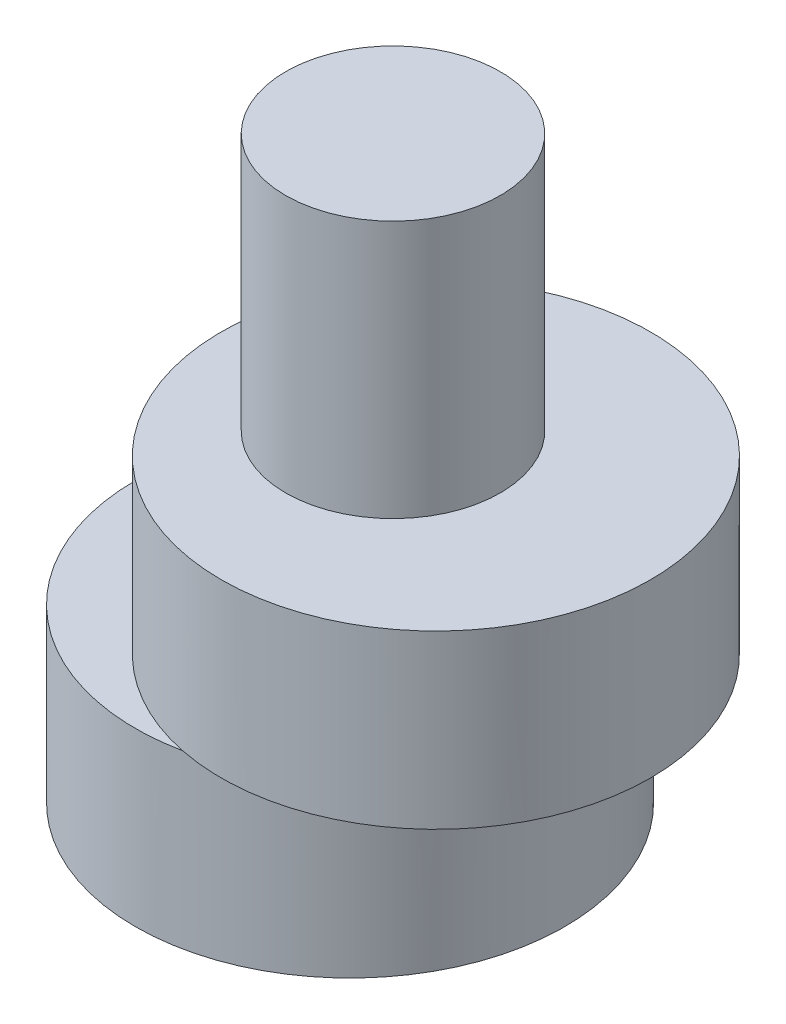
SolidWorks part; units mm, degrees
ref_plane "Front Plane" through (0, 0, 0) normal (0, 0, 1) x (1, 0, 0)
ref_plane "Top Plane" through (0, 0, 0) normal (0, 1, 0) x (1, 0, 0)
ref_plane "Right Plane" through (0, 0, 0) normal (1, 0, 0) x (0, 0, -1)
sketch "Sketch1" plane through (0, 0, 0) normal (0, 1, 0) x (1, 0, 0)
  line L0 (0, 0) -> (-1, 0) construction
  circle A0 centre (0, 0) radius 3
  circle A1 centre (-1, 0) radius 5
  dimension "D1" = 6
  dimension "D3" = 10
  dimension "D2" = 1
extrude "Boss-Extrude1" add sketch "Sketch1" along normal blind 4
sketch "Sketch2" plane through (0, 4, 0) normal (0, 1, 0) x (1, 0, 0)
  line L0 (0, 0) -> (1, 0) construction
  circle A0 centre (1, 0) radius 5
  dimension "D2" = 10
  dimension "D1" = 1
extrude "Boss-Extrude2" add sketch "Sketch2" along normal blind 4
sketch "Sketch3" plane through (0, 8, 0) normal (0, 1, 0) x (1, 0, 0)
  circle A0 centre (0, 0) radius 2.5
  dimension "D1" = 5
extrude "Boss-Extrude3" add sketch "Sketch3" along normal blind 6
sketch "Sketch4" plane through (0, 4, 0) normal (0, -1, 0) x (1, 0, 0)
  circle A0 centre (0, 0) radius 3
extrude "Cut-Extrude1" cut sketch "Sketch4" against normal blind 2
sketch "Sketch6" plane through (0, 6, 0) normal (0, -1, 0) x (1, 0, 0)
  line L0 (1.9, 2.3216) -> (1.9, -2.3216)
  line L1 (0, 0) -> (3, 0) construction
  circle A0 centre (0, 0) radius 3
  circle M4 centre (0, 0) radius 3
  dimension "D2" = 6
  dimension "D1" = 1.9
extrude "Boss-Extrude4" add sketch "Sketch6" along normal through all contours L1 L0 M4 | L0 L1 A0
